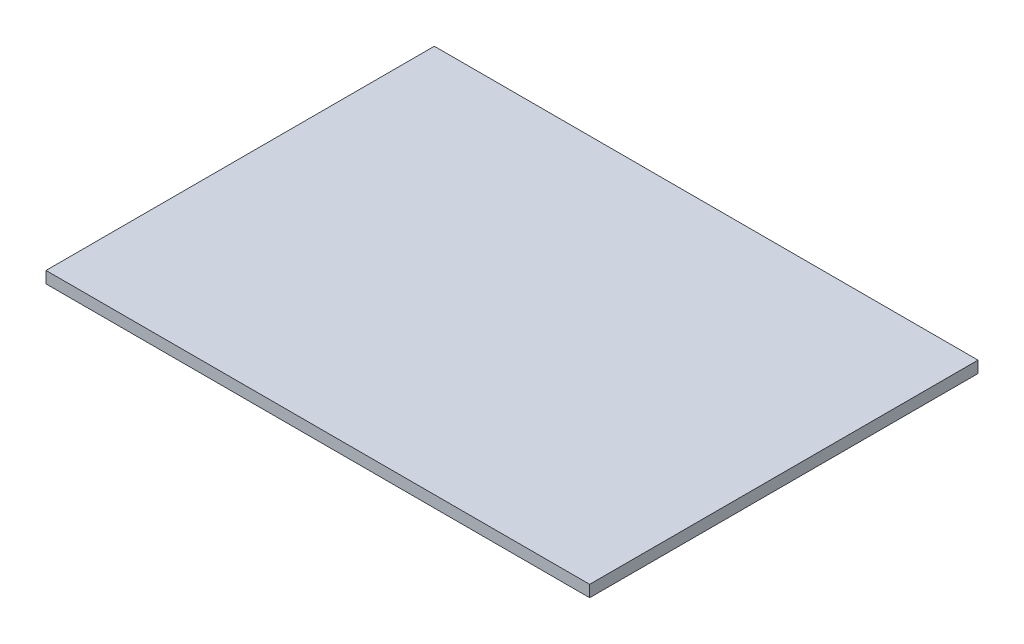
SolidWorks part; units mm, degrees
ref_plane "Plano frontal" through (0, 0, 0) normal (0, 0, 1) x (1, 0, 0)
ref_plane "Plano superior" through (0, 0, 0) normal (0, 1, 0) x (1, 0, 0)
ref_plane "Plano direito" through (0, 0, 0) normal (1, 0, 0) x (0, 0, -1)
sketch "Esboço1" plane through (0, 0, 0) normal (0, 1, 0) x (1, 0, 0)
  line L1 (-35, -25) -> (35, -25)
  line L2 (-35, -25) -> (-35, 25)
  line L3 (-35, 25) -> (35, 25)
  line L4 (35, -25) -> (35, 25)
  line L5 (-35, -25) -> (35, 25) construction
  line L6 (-35, 25) -> (35, -25) construction
  point P0 (0, 0)
  dimension "D1" = 70
  dimension "D2" = 50
extrude "Ressalto-extrusão1" add sketch "Esboço1" along normal blind 1.5
